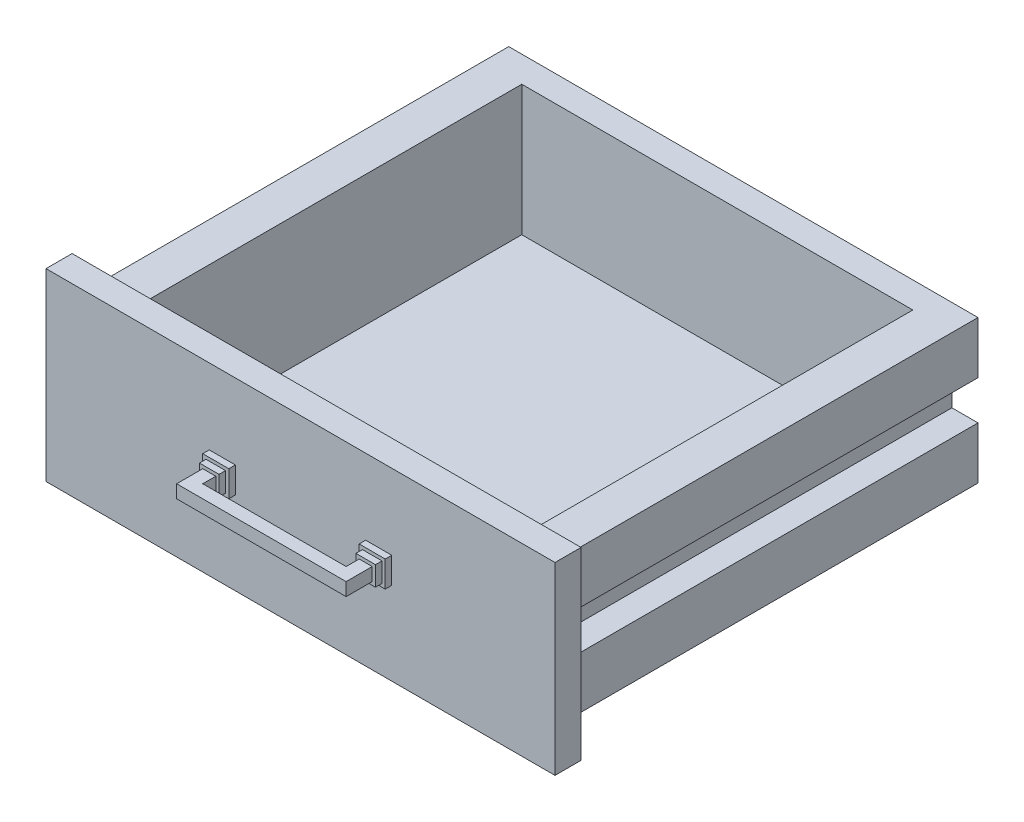
SolidWorks part; units mm, degrees
ref_plane "Front Plane" through (0, 0, 0) normal (0, 0, 1) x (1, 0, 0)
ref_plane "Top Plane" through (0, 0, 0) normal (0, 1, 0) x (1, 0, 0)
ref_plane "Right Plane" through (0, 0, 0) normal (1, 0, 0) x (0, 0, -1)
sketch "Sketch1" plane through (0, 0, 0) normal (0, 0, 1) x (1, 0, 0)
  line L12 (-180.246, 55.7379) -> (179.754, 55.7379)
  line L13 (179.754, 55.7379) -> (179.754, 15.7379)
  line L14 (179.754, 15.7379) -> (159.754, 15.7379)
  line L15 (159.754, 15.7379) -> (159.754, -14.2621)
  line L16 (179.754, -14.2621) -> (159.754, -14.2621)
  line L17 (179.754, -14.2621) -> (179.754, -54.2621)
  line L18 (-180.246, -54.2621) -> (179.754, -54.2621)
  line L19 (-180.246, -14.2621) -> (-180.246, -54.2621)
  line L20 (-180.246, -14.2621) -> (-160.246, -14.2621)
  line L21 (-160.246, 15.7379) -> (-160.246, -14.2621)
  line L22 (-180.246, 15.7379) -> (-160.246, 15.7379)
  line L23 (-180.246, 55.7379) -> (-180.246, 15.7379)
extrude "Boss-Extrude1" add sketch "Sketch1" against normal blind 320 contours L12 L13 L14 L15 L16 L17 L18 L19 L20 L21 L22 L23
sketch "Sketch2" plane through (0, 0, 0) normal (0, 0, 1) x (1, 0, 0)
  line L0 (-180.246, 55.7379) -> (179.754, 55.7379) construction
  line L1 (195.246, -70.7379) -> (-195.246, -70.7379)
  line L2 (195.246, -70.7379) -> (195.246, 70.7379)
  line L3 (195.246, 70.7379) -> (-195.246, 70.7379)
  line L4 (-195.246, -70.7379) -> (-195.246, 70.7379)
  line L5 (195.246, -70.7379) -> (-195.246, 70.7379) construction
  line L6 (195.246, 70.7379) -> (-195.246, -70.7379) construction
  line L7 (-180.246, 55.7379) -> (-180.246, 15.7379) construction
  point P0 (0, 0)
  dimension "D1" = 15
  dimension "D2" = 15
extrude "Boss-Extrude2" add sketch "Sketch2" along normal blind 20
sketch "Sketch4" plane through (0, 55.7379, 0) normal (0, 1, 0) x (1, 0, 0)
  line L0 (-180.246, 0) -> (179.754, 0) construction
  line L1 (149.754, 0) -> (-150.246, 0)
  line L2 (149.754, 0) -> (149.754, 300)
  line L3 (149.754, 300) -> (-150.246, 300)
  line L4 (-150.246, 0) -> (-150.246, 300)
  line L5 (179.754, 320) -> (179.754, 0) construction
  line L6 (-180.246, 320) -> (-180.246, 0) construction
  line L7 (-180.246, 320) -> (179.754, 320) construction
  dimension "D1" = 30
  dimension "D2" = 30
  dimension "D3" = 20
extrude "Cut-Extrude1" cut sketch "Sketch4" against normal blind 100
sketch "Sketch5" plane through (0, 0, 20) normal (0, 0, 1) x (1, 0, 0)
  line L1 (-50, -7.0875) -> (-70, -7.0875)
  line L2 (-50, -7.0875) -> (-50, 12.9125)
  line L3 (-50, 12.9125) -> (-70, 12.9125)
  line L4 (-70, -7.0875) -> (-70, 12.9125)
  line L5 (-50, -7.0875) -> (-70, 12.9125) construction
  line L6 (-50, 12.9125) -> (-70, -7.0875) construction
  line L7 (0, 92.6994) -> (0, -92.3835) construction
  line L8 (50, 12.9125) -> (70, 12.9125)
  line L9 (70, -7.0875) -> (70, 12.9125)
  line L10 (50, -7.0875) -> (70, -7.0875)
  line L11 (50, -7.0875) -> (50, 12.9125)
  point P0 (-60, 2.9125)
  point P5 (-50, 2.9125)
  dimension "D1" = 20
  dimension "D2" = 20
  dimension "D3" = 50
extrude "Boss-Extrude3" add sketch "Sketch5" along normal blind 5
sketch "Sketch6" plane through (0, 0, 25) normal (0, 0, 1) x (1, 0, 0)
  line L0 (-50, 12.9125) -> (-70, 12.9125) construction
  line L1 (-52.5, 10.4125) -> (-67.5, 10.4125)
  line L2 (-52.5, 10.4125) -> (-52.5, -4.5875)
  line L3 (-52.5, -4.5875) -> (-67.5, -4.5875)
  line L4 (-67.5, 10.4125) -> (-67.5, -4.5875)
  line L5 (-52.5, 10.4125) -> (-67.5, -4.5875) construction
  line L6 (-52.5, -4.5875) -> (-67.5, 10.4125) construction
  line L7 (-50, -7.0875) -> (-50, 12.9125) construction
  line L8 (0, 112.5078) -> (0, -103.0262) construction
  line L9 (52.5, -4.5875) -> (67.5, -4.5875)
  line L10 (67.5, 10.4125) -> (67.5, -4.5875)
  line L11 (52.5, 10.4125) -> (67.5, 10.4125)
  line L12 (52.5, 10.4125) -> (52.5, -4.5875)
  point P0 (-60, 2.9125)
  dimension "D1" = 15
  dimension "D2" = 15
  dimension "D3" = 2.5
  dimension "D4" = 2.5
extrude "Boss-Extrude4" add sketch "Sketch6" along normal blind 5
sketch "Sketch7" plane through (0, 0, 30) normal (0, 0, 1) x (1, 0, 0)
  line L0 (-52.5, 10.4125) -> (-67.5, 10.4125) construction
  line L1 (-55, 7.9125) -> (-65, 7.9125)
  line L2 (-55, 7.9125) -> (-55, -2.0875)
  line L3 (-55, -2.0875) -> (-65, -2.0875)
  line L4 (-65, 7.9125) -> (-65, -2.0875)
  line L5 (-55, 7.9125) -> (-65, -2.0875) construction
  line L6 (-55, -2.0875) -> (-65, 7.9125) construction
  line L7 (-52.5, -4.5875) -> (-52.5, 10.4125) construction
  line L8 (0, 82.7256) -> (0, -94.975) construction
  line L9 (55, -2.0875) -> (65, -2.0875)
  line L10 (65, 7.9125) -> (65, -2.0875)
  line L11 (55, 7.9125) -> (65, 7.9125)
  line L12 (55, 7.9125) -> (55, -2.0875)
  point P0 (-60, 2.9125)
  dimension "D1" = 10
  dimension "D2" = 10
  dimension "D3" = 2.5
  dimension "D4" = 2.5
extrude "Boss-Extrude6" add sketch "Sketch7" along normal blind 20
sketch "Sketch8" plane through (55, 0, 0) normal (-1, 0, 0) x (0, 0, 1)
  line L0 (50, 7.9125) -> (40, 7.9125)
  line L1 (50, 7.9125) -> (50, -2.0875)
  line L2 (50, -2.0875) -> (40, -2.0875)
  line L3 (40, 7.9125) -> (40, -2.0875)
  line L4 (50, 7.9125) -> (40, -2.0875) construction
  line L5 (50, -2.0875) -> (40, 7.9125) construction
  line L6 (50, 7.9125) -> (50, -2.0875) construction
  line L7 (50, 7.9125) -> (30, 7.9125) construction
  point P0 (45, 2.9125)
  dimension "D1" = 10
  dimension "D2" = 10
extrude "Boss-Extrude7" add sketch "Sketch8" along normal up to next
